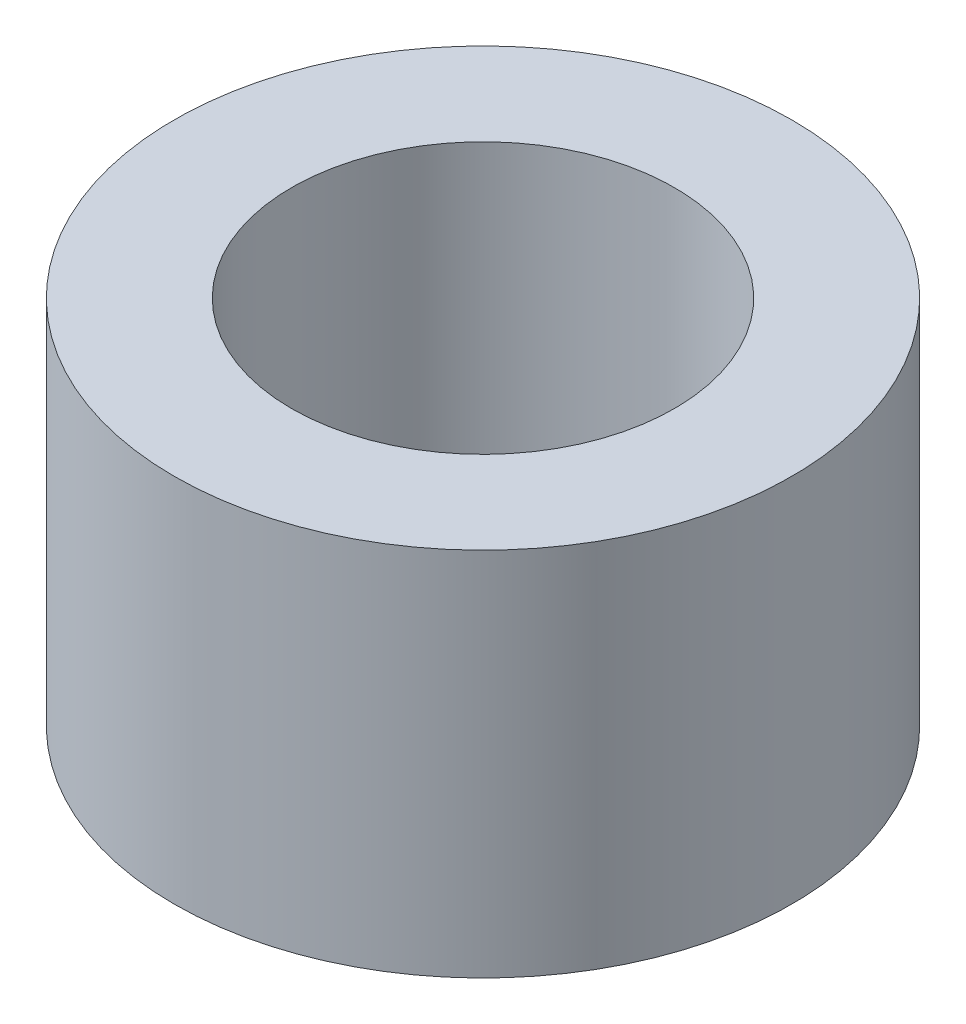
SolidWorks part; units mm, degrees
material "6061 合金"
ref_plane "前视基准面" through (0, 0, 0) normal (0, 0, 1) x (1, 0, 0)
ref_plane "上视基准面" through (0, 0, 0) normal (0, 1, 0) x (1, 0, 0)
ref_plane "右视基准面" through (0, 0, 0) normal (1, 0, 0) x (0, 0, -1)
sketch "草图1" plane through (0, 0, 0) normal (0, 1, 0) x (1, 0, 0)
  circle A0 centre (0, 0) radius 1.55
  circle A1 centre (0, 0) radius 2.5
  dimension "D1" = 5
  dimension "D2" = 3.1
extrude "凸台-拉伸1" add sketch "草图1" along normal blind 3
